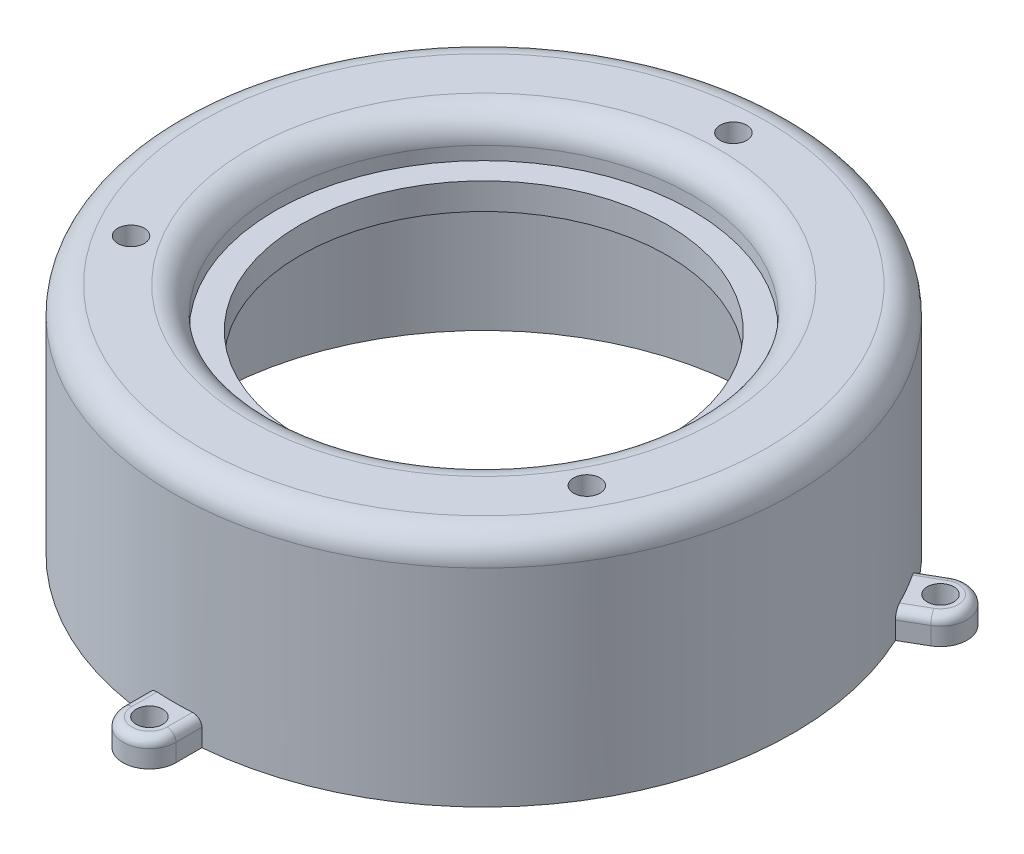
SolidWorks part; units mm, degrees
ref_plane "Front Plane" through (0, 0, 0) normal (0, 0, 1) x (1, 0, 0)
ref_plane "Top Plane" through (0, 0, 0) normal (0, 1, 0) x (1, 0, 0)
ref_plane "Right Plane" through (0, 0, 0) normal (1, 0, 0) x (0, 0, -1)
sketch "Sketch1" plane through (0, 0, 0) normal (0, 1, 0) x (1, 0, 0)
  line L0 (0, 0) -> (-8.3501, 15.3794) construction
  line L1 (0, 0) -> (-9.1439, -14.9211) construction
  line L2 (0, 0) -> (17.494, -0.4583) construction
  circle A0 centre (0, 0) radius 35
  circle A1 centre (-8.3501, 15.3794) radius 2.6
  circle A2 centre (-9.1439, -14.9211) radius 2.6
  circle A3 centre (17.494, -0.4583) radius 2.6
  circle A4 centre (0, 0) radius 17.5 construction
  circle A5 centre (0, 0) radius 11
  dimension "D1" = 35
  dimension "D2" = 5.2
  dimension "D5" = 70
  dimension "D6" = 22
  dimension "D3" = 120
  dimension "D4" = 120
extrude "Boss-Extrude1" add sketch "Sketch1" along normal blind 50
sketch "Sketch2" plane through (0, 0, 0) normal (0, -1, 0) x (1, 0, 0)
  circle A0 centre (0, 0) radius 31
  dimension "D1" = 62
extrude "Cut-Extrude1" cut sketch "Sketch2" against normal blind 45
sketch "Sketch3" plane through (0, 50, 0) normal (0, 1, 0) x (1, 0, 0)
  circle A0 centre (0, 0) radius 23.55
  circle A1 centre (0, 0.7165) radius 26.05
  dimension "D1" = 47.1
  dimension "D2" = 52.1
extrude "Boss-Extrude2" add sketch "Sketch3" along normal blind 7.5
sketch "Sketch5" plane through (0, 57.5, 0) normal (0, 1, 0) x (1, 0, 0)
  circle A0 centre (0, 0) radius 20.75
  circle A1 centre (0, 0) radius 23.55
  circle A4 centre (0, 0) radius 23.55 construction
  dimension "D1" = 41.5
extrude "Boss-Extrude3" add sketch "Sketch5" along normal blind 2 from offset 8 offset against normal yes
sketch "Sketch7" plane through (0, 50, 0) normal (0, 1, 0) x (1, 0, 0)
  circle A0 centre (0, 0) radius 25.3335
  circle A1 centre (0, 0) radius 35
  dimension "D1" = 70
extrude "Boss-Extrude4" add sketch "Sketch7" along normal blind 7.5
sketch "Sketch9" plane through (0, 45, 0) normal (0, -1, 0) x (1, 0, 0)
  circle A0 centre (0, 0) radius 26.05
  circle A1 centre (0, 0) radius 31
  dimension "D1" = 52.1
  dimension "D2" = 62
extrude "Cut-Extrude2" cut sketch "Sketch9" against normal blind 10
fillet "Fillet1" radius 3 2 edges at (0, 57.5, 23.55) (0, 57.5, 35)
sketch "Sketch11" plane through (0, 50, 0) normal (0, 1, 0) x (1, 0, 0)
  circle A0 centre (0, 0) radius 26.8835
extrude "Cut-Extrude4" cut sketch "Sketch11" against normal blind 404
sketch "Sketch12" plane through (0, 57.5, 0) normal (0, 1, 0) x (1, 0, 0)
  line L0 (0, 0) -> (-0.7629, 28.99) construction
  circle A0 centre (-0.7629, 28.99) radius 1.5
  dimension "D2" = 3
  dimension "D1" = 29
extrude "Cut-Extrude5" cut sketch "Sketch12" against normal blind 7
sketch "Sketch13" plane through (0, 55, 0) normal (0, -1, 0) x (1, 0, 0)
  line L7 (-3.9959, -28.9592) -> (-2.4061, -31.7745)
  line L8 (-2.4061, -31.7745) -> (0.827, -31.8052)
  line L9 (0.827, -31.8052) -> (2.4701, -29.0207)
  line L10 (2.4701, -29.0207) -> (0.8802, -26.2055)
  line L11 (0.8802, -26.2055) -> (-2.3528, -26.1747)
  line L12 (-2.3528, -26.1747) -> (-3.9959, -28.9592)
  circle A0 centre (-0.7629, -28.99) radius 2.8 construction
  circle A4 centre (-0.7629, -28.99) radius 1.5 construction
  dimension "D1" = 5.6
extrude "Cut-Extrude6" cut sketch "Sketch13" along normal blind 7
pattern_circular "CirPattern1" count 3 every 120 about axis through (0, 0, 0) along (0, 1, 0) of "Cut-Extrude5", "Cut-Extrude6"
sketch "Sketch15" plane through (0, 50, 0) normal (0, -1, 0) x (1, 0, 0)
  circle A0 centre (0, 0) radius 26.05
  circle A1 centre (0, 0) radius 26.05 construction
  circle A2 centre (0, 0) radius 26.05 construction
  circle A3 centre (0, 0) radius 20.75
  circle A5 centre (0, 0) radius 20.75 construction
extrude "Boss-Extrude5" add sketch "Sketch15" against normal blind 3
sketch "Sketch10" plane through (0, 0, 0) normal (1, 0, 0) x (0, 0, -1)
  line L0 (32, 57.5) -> (-32, 57.5) construction
  line L1 (-73.5817, 31.1) -> (71.1703, 31.1)
  line L2 (-73.5817, 31.1) -> (-73.5817, -17.7411)
  line L3 (-73.5817, -17.7411) -> (71.1703, -17.7411)
  line L4 (71.1703, 31.1) -> (71.1703, -17.7411)
  dimension "D1" = 26.4
extrude "Cut-Extrude7" cut sketch "Sketch10" against normal blind 113 and the other way blind 93
sketch "Sketch16" plane through (0, 31.1, 0) normal (0, -1, 0) x (1, 0, 0)
  line L0 (-3, 34.8712) -> (-3, 37.8)
  line L1 (3, 34.8712) -> (3, 37.8)
  line L2 (-3, 34.8712) -> (3, 34.8712)
  circle A0 centre (0, 0) radius 35 construction
  arc A1 (3, 37.8) -> (-3, 37.8) centre (0, 37.8) ccw
  circle A2 centre (0, 37.8) radius 1.5
  dimension "D1" = 3
  dimension "D2" = 3
  dimension "D3" = 37.8
extrude "Boss-Extrude6" add sketch "Sketch16" against normal blind 3
fillet "Fillet3" radius 1 3 edges at (3, 34.1, 36.3356) (0, 34.1, 40.8) (-3, 34.1, 36.3356)
pattern_circular "CirPattern7" count 3 every 120 about axis through (0, 0, 0) along (0, 1, 0) of "Boss-Extrude6", "Fillet3"
